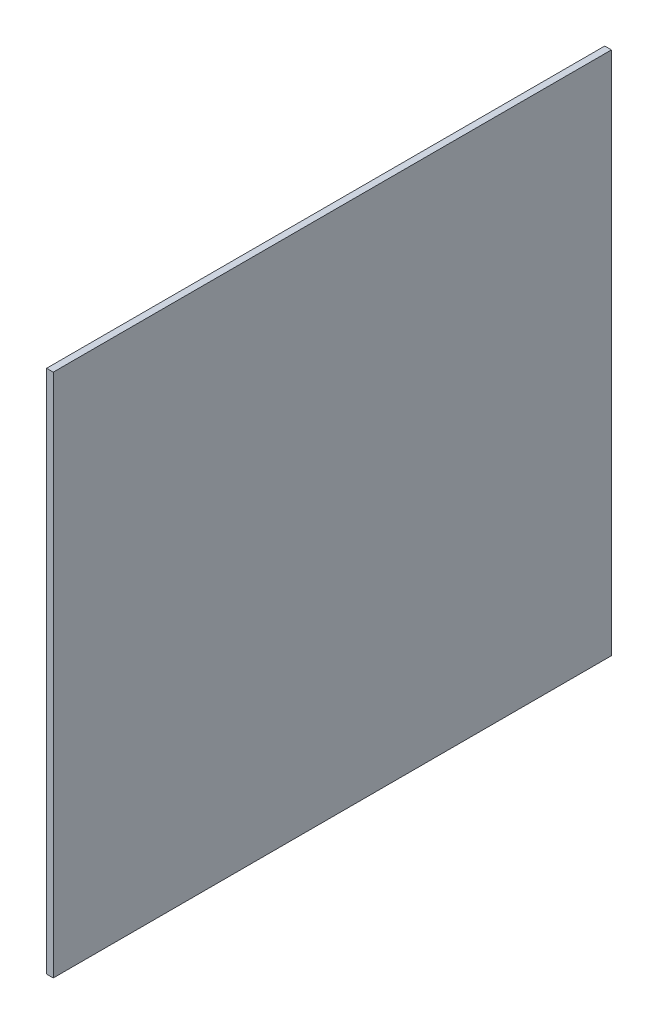
SolidWorks part; units mm, degrees
ref_plane "Front Plane" through (0, 0, 0) normal (0, 0, 1) x (1, 0, 0)
ref_plane "Top Plane" through (0, 0, 0) normal (0, 1, 0) x (1, 0, 0)
ref_plane "Right Plane" through (0, 0, 0) normal (1, 0, 0) x (0, 0, -1)
sketch "Sketch1" plane through (0, 0, 0) normal (1, 0, 0) x (0, 0, -1)
  line L1 (-2500, 2350) -> (2500, 2350)
  line L2 (-2500, 2350) -> (-2500, -2350)
  line L3 (-2500, -2350) -> (2500, -2350)
  line L4 (2500, 2350) -> (2500, -2350)
  line L5 (-2500, 2350) -> (2500, -2350) construction
  line L6 (-2500, -2350) -> (2500, 2350) construction
  point P0 (0, 0)
  dimension "D1" = 5000
  dimension "D2" = 4700
extrude "Boss-Extrude1" add sketch "Sketch1" along normal blind 60
